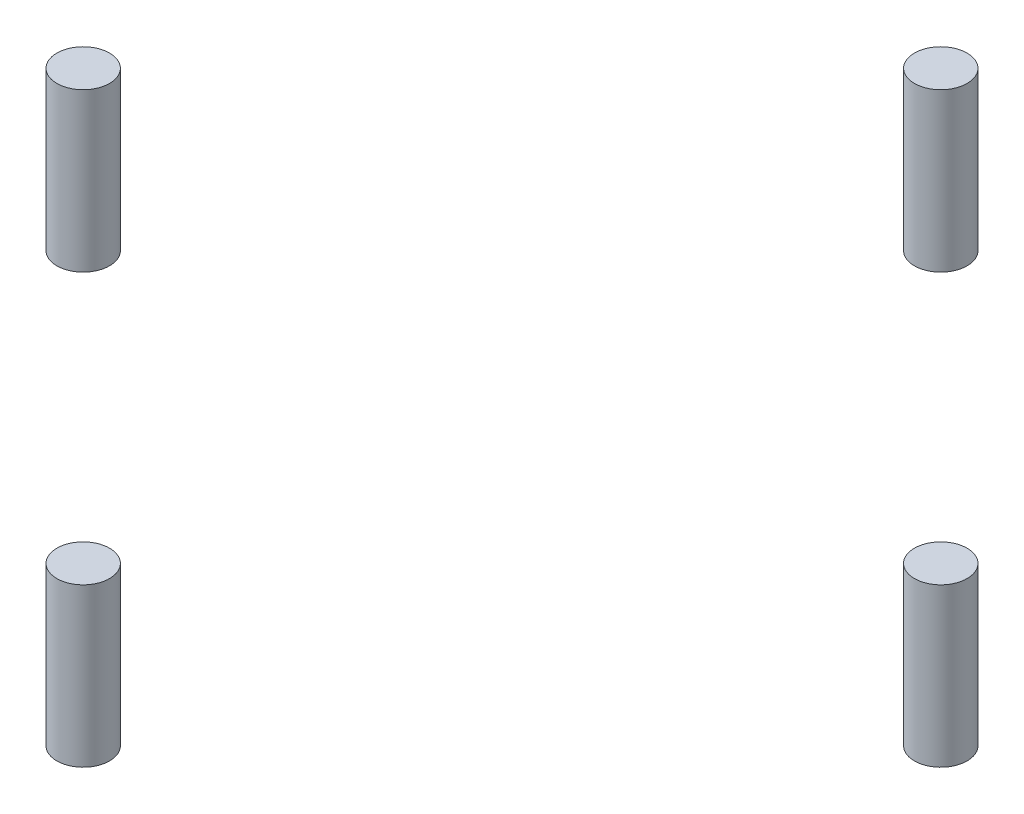
SolidWorks part; units mm, degrees
ref_plane "前视基准面" through (0, 0, 0) normal (0, 0, 1) x (1, 0, 0)
ref_plane "上视基准面" through (0, 0, 0) normal (0, 1, 0) x (1, 0, 0)
ref_plane "右视基准面" through (0, 0, 0) normal (1, 0, 0) x (0, 0, -1)
sketch "草图1" plane through (0, 0, 0) normal (0, 1, 0) x (1, 0, 0)
  line L1 (39.4264, 36.598) -> (16.3284, 13.5)
  line L4 (42.4264, 36.4264) -> (42.4264, 37.9264) construction
  line L5 (41.4264, 36.4264) -> (41.4264, 37.9264)
  line L10 (43.4264, 36.4264) -> (43.4264, 37.9264)
  line L13 (42.4264, 36.4264) -> (42.4264, 37.9264) construction
  line L17 (39.4264, 36.4264) -> (39.4264, 36.598)
  line L24 (45.4264, 36.4264) -> (45.4264, 39.4264)
  line L28 (48.4264, 42.4264) -> (46.9264, 42.4264) construction
  line L31 (48.4264, 39.4264) -> (45.4264, 39.4264)
  line L33 (48.4264, 45.4264) -> (45.4264, 45.4264)
  line L34 (48.4264, 42.4264) -> (46.9264, 42.4264) construction
  line L35 (48.4264, 43.4264) -> (46.9264, 43.4264)
  line L44 (48.4264, 41.4264) -> (46.9264, 41.4264)
  line L45 (42.4264, 48.4264) -> (42.4264, 46.9264) construction
  line L48 (36.4264, 42.4264) -> (37.9264, 42.4264) construction
  line L51 (45.4264, 48.4264) -> (45.4264, 45.4264)
  line L54 (39.4264, 48.4264) -> (39.4264, 45.4264)
  line L57 (36.4264, 45.4264) -> (39.4264, 45.4264)
  line L58 (36.4264, 39.4264) -> (36.598, 39.4264)
  line L59 (42.4264, 48.4264) -> (42.4264, 46.9264) construction
  line L62 (43.4264, 48.4264) -> (43.4264, 46.9264)
  line L63 (41.4264, 48.4264) -> (41.4264, 46.9264)
  line L64 (36.4264, 42.4264) -> (37.9264, 42.4264) construction
  line L65 (36.4264, 41.4264) -> (37.9264, 41.4264)
  line L66 (36.4264, 43.4264) -> (37.9264, 43.4264)
  line L67 (17.1716, 44.229) -> (33.5024, 41.7553)
  line L68 (0, 42) -> (10, 42)
  line L69 (0, 40) -> (10, 40)
  line L70 (0, 1) -> (0, 5)
  line L71 (0, 1) -> (10, 1)
  line L72 (0, -1) -> (10, -1)
  line L73 (-1, 0) -> (-4.9453, 0)
  line L77 (7.5, 5) -> (0, 5)
  line L78 (48.4035, 2.9662) -> (43.7435, 33.731)
  line L84 (36.598, 39.4264) -> (17.1716, 20)
  line L85 (36.4264, -42.4264) -> (37.9264, -42.4264) construction
  line L87 (42.4264, -48.4264) -> (42.4264, -46.9264) construction
  line L88 (48.4264, -42.4264) -> (46.9264, -42.4264) construction
  line L89 (42.4264, -36.4264) -> (42.4264, -37.9264) construction
  line L92 (41.7553, -33.5024) -> (46.5405, -1.9113)
  line L94 (41.7553, 33.5024) -> (46.5405, 1.9113)
  line L95 (17.1716, 20) -> (17.1716, 44.229)
  line L96 (48.4035, -2.9662) -> (43.7435, -33.731)
  line L98 (36.4264, -39.4264) -> (36.598, -39.4264)
  line L99 (36.4264, -45.4264) -> (39.4264, -45.4264)
  line L100 (39.4264, -48.4264) -> (39.4264, -45.4264)
  line L101 (45.4264, -48.4264) -> (45.4264, -45.4264)
  line L102 (48.4264, -45.4264) -> (45.4264, -45.4264)
  line L103 (48.4264, -39.4264) -> (45.4264, -39.4264)
  line L104 (45.4264, -36.4264) -> (45.4264, -39.4264)
  line L105 (39.4264, -36.4264) -> (39.4264, -36.598)
  line L106 (39.4264, -36.598) -> (16.3284, -13.5)
  line L107 (36.4264, -42.4264) -> (37.9264, -42.4264) construction
  line L108 (36.4264, -41.4264) -> (37.9264, -41.4264)
  line L109 (36.4264, -43.4264) -> (37.9264, -43.4264)
  line L110 (42.4264, -48.4264) -> (42.4264, -46.9264) construction
  line L111 (43.4264, -48.4264) -> (43.4264, -46.9264)
  line L112 (41.4264, -48.4264) -> (41.4264, -46.9264)
  line L113 (48.4264, -42.4264) -> (46.9264, -42.4264) construction
  line L114 (48.4264, -43.4264) -> (46.9264, -43.4264)
  line L115 (48.4264, -41.4264) -> (46.9264, -41.4264)
  line L116 (42.4264, -36.4264) -> (42.4264, -37.9264) construction
  line L117 (41.4264, -36.4264) -> (41.4264, -37.9264)
  line L118 (43.4264, -36.4264) -> (43.4264, -37.9264)
  line L119 (33.731, 43.7435) -> (2.9661, 48.4035)
  line L120 (0, 51.8528) -> (0, 50.3528)
  line L125 (0, 47.3528) -> (0, 42)
  line L126 (0, -47.3528) -> (0, -44.4131)
  line L127 (0, -51.8528) -> (0, -50.3528)
  line L128 (33.731, -43.7435) -> (2.9661, -48.4035)
  line L129 (17.1716, -44.229) -> (33.5024, -41.7553)
  line L130 (17.1716, -20) -> (17.1716, -44.229)
  line L131 (36.598, -39.4264) -> (17.1716, -20)
  line L132 (36.4264, -39.4264) -> (36.598, -39.4264)
  line L133 (0, -29.3528) -> (10, -29.3528)
  line L135 (10, -43.3528) -> (3, -44.4131)
  line L137 (3, -44.4131) -> (0, -44.4131)
  line L138 (10, -29.3528) -> (10, -43.3528)
  line L139 (0, -29.3528) -> (0, -1)
  line L140 (8.5, 34) -> (8.5, 20) construction
  line L141 (10, 34) -> (10, 20)
  line L142 (7, 34) -> (7, 20)
  line L143 (3.5, 34) -> (3.5, 15) construction
  line L144 (5, 34) -> (5, 15)
  line L145 (2, 34) -> (2, 15)
  line L146 (16.3284, 13.5) -> (16.3284, -13.5)
  line L148 (7.5, 7) -> (0, 7)
  line L149 (0, 7) -> (0, 40)
  circle A48 centre (10, 10) radius 1
  circle A49 centre (12.5, 12.5) radius 1
  arc A52 (41.4264, 36.4264) -> (43.4264, 36.4264) centre (42.4264, 36.4264) ccw
  arc A53 (43.4264, 37.9264) -> (41.4264, 37.9264) centre (42.4264, 37.9264) ccw
  arc A54 (39.4264, 36.4264) -> (41.7553, 33.5024) centre (42.4264, 36.4264) ccw
  arc A56 (48.4264, 45.4264) -> (48.4264, 39.4264) centre (48.4264, 42.4264) cw
  arc A57 (48.4264, 43.4264) -> (48.4264, 41.4264) centre (48.4264, 42.4264) cw
  arc A58 (46.9264, 41.4264) -> (46.9264, 43.4264) centre (46.9264, 42.4264) cw
  arc A59 (45.4264, 48.4264) -> (39.4264, 48.4264) centre (42.4264, 48.4264) ccw
  arc A61 (43.4264, 48.4264) -> (41.4264, 48.4264) centre (42.4264, 48.4264) ccw
  arc A62 (41.4264, 46.9264) -> (43.4264, 46.9264) centre (42.4264, 46.9264) ccw
  arc A63 (36.4264, 41.4264) -> (36.4264, 43.4264) centre (36.4264, 42.4264) cw
  arc A64 (37.9264, 43.4264) -> (37.9264, 41.4264) centre (37.9264, 42.4264) cw
  circle A65 centre (42.4264, 42.4264) radius 2.5
  arc A69 (10, 40) -> (10, 42) centre (10, 41) ccw
  arc A71 (10, -1) -> (10, 1) centre (10, 0) ccw
  arc A76 (33.5024, 41.7553) -> (36.4264, 39.4264) centre (36.4264, 42.4264) ccw
  arc A77 (33.5024, -43.0975) -> (36.4264, -45.4264) centre (36.4264, -42.4264) ccw
  arc A79 (0, 50.3528) -> (0, 47.3528) centre (0, 48.8528) cw
  arc A80 (2.9661, 48.4035) -> (0, 51.8528) centre (0, 48.8528) ccw
  circle A81 centre (42.4264, -42.4264) radius 2.5
  arc A82 (36.4264, -39.4264) -> (33.731, -41.1093) centre (36.4264, -42.4264) ccw
  arc A83 (45.4264, -48.4264) -> (39.4264, -48.4264) centre (42.4264, -48.4264) cw
  arc A84 (48.4264, -45.4264) -> (48.4264, -39.4264) centre (48.4264, -42.4264) ccw
  arc A85 (39.4264, -36.4264) -> (41.7553, -33.5024) centre (42.4264, -36.4264) cw
  circle A86 centre (12.5, -12.5) radius 1
  circle A87 centre (10, -10) radius 1
  arc A88 (36.4264, -41.4264) -> (36.4264, -43.4264) centre (36.4264, -42.4264) ccw
  arc A89 (37.9264, -43.4264) -> (37.9264, -41.4264) centre (37.9264, -42.4264) ccw
  arc A90 (43.4264, -48.4264) -> (41.4264, -48.4264) centre (42.4264, -48.4264) cw
  arc A91 (41.4264, -46.9264) -> (43.4264, -46.9264) centre (42.4264, -46.9264) cw
  arc A92 (48.4264, -43.4264) -> (48.4264, -41.4264) centre (48.4264, -42.4264) ccw
  arc A93 (46.9264, -41.4264) -> (46.9264, -43.4264) centre (46.9264, -42.4264) ccw
  arc A94 (41.4264, -36.4264) -> (43.4264, -36.4264) centre (42.4264, -36.4264) cw
  arc A95 (43.4264, -37.9264) -> (41.4264, -37.9264) centre (42.4264, -37.9264) cw
  circle A99 centre (48.8528, 0) radius 1.5
  arc A101 (48.4035, -2.9662) -> (48.4035, 2.9662) centre (48.8528, 0) ccw
  arc A102 (43.7435, 33.731) -> (45.4264, 36.4264) centre (42.4264, 36.4264) ccw
  arc A103 (46.5405, 1.9113) -> (46.5405, -1.9113) centre (48.8528, 0) ccw
  arc A104 (43.7435, -33.731) -> (45.4264, -36.4264) centre (42.4264, -36.4264) cw
  arc A105 (36.4264, 45.4264) -> (33.731, 43.7435) centre (36.4264, 42.4264) ccw
  arc A106 (2.9661, -48.4035) -> (0, -51.8528) centre (0, -48.8528) cw
  arc A107 (0, -50.3528) -> (0, -47.3528) centre (0, -48.8528) ccw
  arc A108 (33.5024, -41.7553) -> (36.4264, -39.4264) centre (36.4264, -42.4264) cw
  circle A109 centre (10, -26.3528) radius 1.5
  arc A110 (10, 34) -> (7, 34) centre (8.5, 34) ccw
  arc A111 (7, 20) -> (10, 20) centre (8.5, 20) ccw
  arc A112 (5, 34) -> (2, 34) centre (3.5, 34) ccw
  arc A113 (2, 15) -> (5, 15) centre (3.5, 15) ccw
  arc A114 (7.5, 5) -> (7.5, 7) centre (7.5, 6) ccw
  circle A115 centre (0, -48.8528) radius 3
  circle A116 centre (0, 48.8528) radius 3
  circle A117 centre (48.8528, 0) radius 3
  circle A118 centre (-48.8528, 0) radius 3
  point P0 (8.5, 27)
  point P11 (42.4264, 37.1764)
  point P16 (42.4264, 37.1764)
  point P28 (47.6764, 42.4264)
  point P29 (47.6764, 42.4264)
  point P44 (5, 30)
  point P47 (42.4264, 47.6764)
  point P48 (37.1764, 42.4264)
  point P49 (42.4264, 47.6764)
  point P54 (37.1764, 42.4264)
  point P63 (5, 0)
  point P118 (15.3284, 0)
  point P127 (37.1764, -42.4264)
  point P134 (42.4264, -47.6764)
  point P139 (47.6764, -42.4264)
  point P144 (42.4264, -37.1764)
  point P145 (42.4264, -37.1764)
  point P166 (3.75, 4)
  point P167 (3.5, 24.5)
extrude "凸台-拉伸1" add sketch "草图1" along normal blind 18 contours A118 | A116 | A115 | A117
